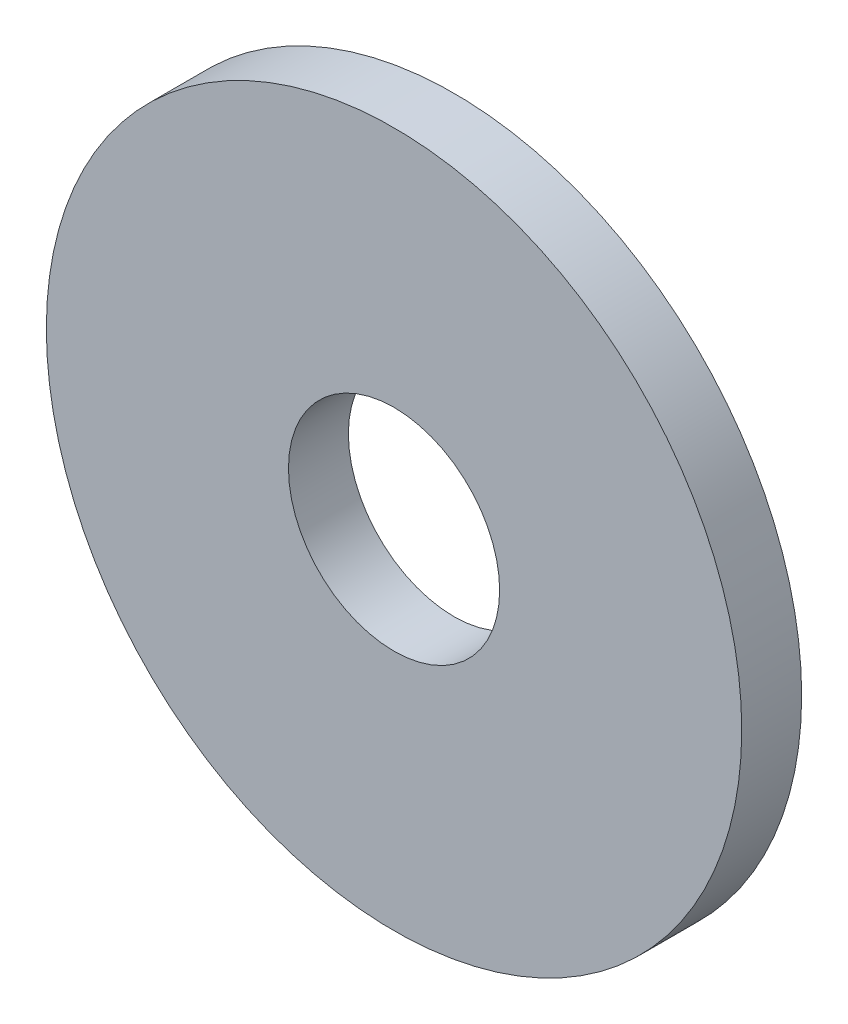
SolidWorks part; units mm, degrees
ref_plane "Front Plane" through (0, 0, 0) normal (0, 0, 1) x (1, 0, 0)
ref_plane "Top Plane" through (0, 0, 0) normal (0, 1, 0) x (1, 0, 0)
ref_plane "Right Plane" through (0, 0, 0) normal (1, 0, 0) x (0, 0, -1)
sketch "Sketch1" plane through (0, 0, 0) normal (0, 0, 1) x (1, 0, 0)
  circle A0 centre (0, 0) radius 7.08
  circle A1 centre (0, 0) radius 2.15
  dimension "D1" = 14.16
  dimension "D2" = 4.3
extrude "Boss-Extrude1" add sketch "Sketch1" along normal mid plane 1.22
